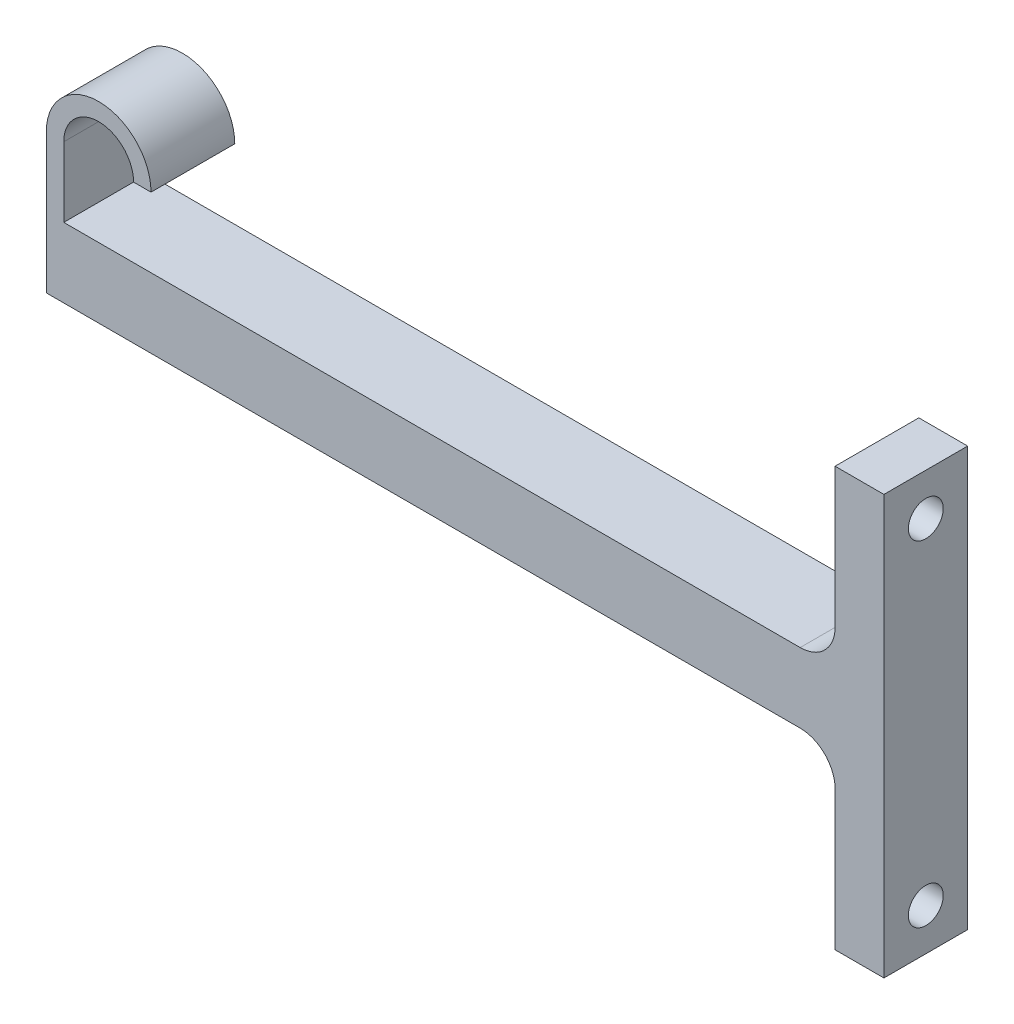
SolidWorks part; units mm, degrees
ref_plane "Front Plane" through (0, 0, 0) normal (0, 0, 1) x (1, 0, 0)
ref_plane "Top Plane" through (0, 0, 0) normal (0, 1, 0) x (1, 0, 0)
ref_plane "Right Plane" through (0, 0, 0) normal (1, 0, 0) x (0, 0, -1)
sketch "Sketch1" plane through (0, 0, 0) normal (0, 0, 1) x (1, 0, 0)
  line L0 (120, 35) -> (120, 5)
  line L1 (0, 0) -> (108, 0)
  line L2 (113, 15) -> (113, 35)
  line L3 (113, 35) -> (120, 35)
  line L4 (120, 5) -> (120, -25)
  line L5 (0, 0) -> (0, 20)
  line L6 (2.5, 20) -> (2.5, 10)
  line L7 (2.5, 10) -> (108, 10)
  line L8 (12.5, 20) -> (15, 20)
  line L9 (120, -25) -> (113, -25)
  line L10 (113, -25) -> (113, -5)
  arc A0 (15, 20) -> (0, 20) centre (7.5, 20) ccw
  arc A1 (2.5, 20) -> (12.5, 20) centre (7.5, 20) cw
  arc A2 (113, 15) -> (108, 10) centre (108, 15) cw
  arc A3 (113, -5) -> (108, 0) centre (108, -5) ccw
  dimension "D3" = 5
  dimension "D7" = 5
  dimension "D8" = 10
  dimension "D9" = 5
  dimension "D1" = 7
  dimension "D2" = 5
  dimension "D4" = 10
  dimension "D5" = 2.5
  dimension "D6" = 2.5
  dimension "D10" = 25
  dimension "D11" = 25
  dimension "D12" = 120
extrude "Boss-Extrude1" add sketch "Sketch1" along normal blind 12
sketch "Sketch3" plane through (120, 0, 0) normal (1, 0, 0) x (0, 0, -1)
  line L0 (-12, 35) -> (0, 35) construction
  line L1 (-12, -25) -> (0, -25) construction
  circle A0 centre (-6, 29) radius 2.5
  circle A1 centre (-6, -19) radius 2.5
  point P6 (-6, 35)
  dimension "D1" = 5
  dimension "D2" = 6
  dimension "D3" = 6
extrude "Cut-Extrude2" cut sketch "Sketch3" against normal up to next
chamfer "Chamfer2" distance 2.5 distance2 2.5 2 edges at (113, -19, 3.5) (113, 31.5, 6)
